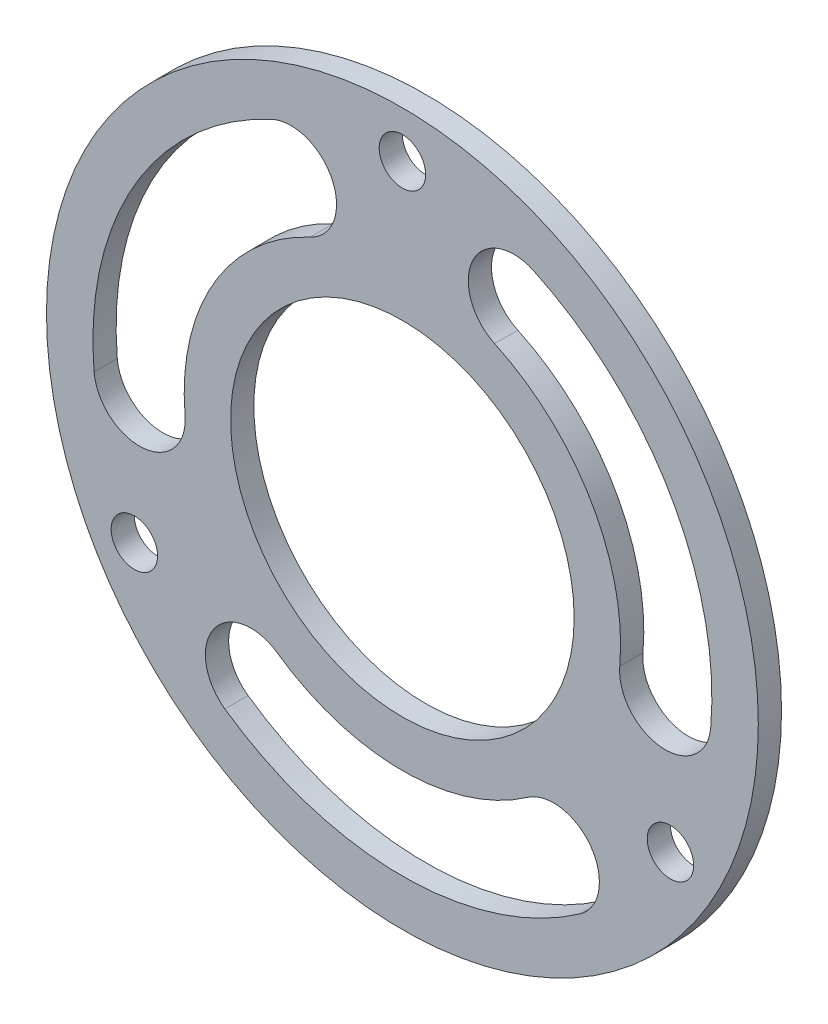
SolidWorks part; units mm, degrees
material "Thornel Mat VMA"
ref_plane "前视基准面" through (0, 0, 0) normal (0, 0, 1) x (1, 0, 0)
ref_plane "上视基准面" through (0, 0, 0) normal (0, 1, 0) x (1, 0, 0)
ref_plane "右视基准面" through (0, 0, 0) normal (1, 0, 0) x (0, 0, -1)
sketch "草图1" plane through (0, 0, 0) normal (0, 0, 1) x (1, 0, 0)
  line L3 (0, 20) -> (0, 0) construction
  circle A0 centre (0, 0) radius 23
  circle A2 centre (0, 20) radius 1.5
  circle A5 centre (0, 0) radius 11.1
  circle A8 centre (0, 0) radius 20 construction
  circle A16 centre (17.3205, -10) radius 1.5
  circle A17 centre (-17.3205, -10) radius 1.5
  dimension "D1" = 46
  dimension "D4" = 3
  dimension "D7" = 3
  dimension "D6" = 22.2
  dimension "D5" = 40
extrude "凸台-拉伸1" add sketch "草图1" along normal blind 1.5
sketch "草图2" plane through (0, 0, 1.5) normal (0, 0, 1) x (1, 0, 0)
  line L0 (0, 0) -> (-16.9851, -1.486) construction
  line L1 (-7.2056, 15.4525) -> (0, 0) construction
  line L2 (-17.3205, -10) -> (0, 0) construction
  line L3 (0, 0) -> (0, 20) construction
  arc A0 (-7.2056, 15.4525) -> (-16.9851, -1.486) centre (0, 0) ccw construction
  arc A1 (-8.4524, 18.1262) -> (-19.9239, -1.7431) centre (0, 0) ccw
  arc A2 (-5.9589, 12.7789) -> (-14.0463, -1.2289) centre (0, 0) ccw
  arc A3 (-5.9589, 12.7789) -> (-8.4524, 18.1262) centre (-7.2056, 15.4525) ccw
  arc A4 (-19.9239, -1.7431) -> (-14.0463, -1.2289) centre (-16.9851, -1.486) ccw
  circle A5 centre (0, 0) radius 11.1 construction
  circle A6 centre (0, 0) radius 23 construction
  arc A7 (16.9851, -1.486) -> (7.2056, 15.4525) centre (0, 0) ccw construction
  arc A20 (19.9239, -1.7431) -> (8.4524, 18.1262) centre (0, 0) ccw
  arc A21 (14.0463, -1.2289) -> (5.9589, 12.7789) centre (0, 0) ccw
  arc A22 (14.0463, -1.2289) -> (19.9239, -1.7431) centre (16.9851, -1.486) ccw
  arc A23 (8.4524, 18.1262) -> (5.9589, 12.7789) centre (7.2056, 15.4525) ccw
  arc A24 (-9.7795, -13.9665) -> (9.7795, -13.9665) centre (0, 0) ccw construction
  arc A25 (-11.4715, -16.383) -> (11.4715, -16.383) centre (0, 0) ccw
  arc A26 (-8.0874, -11.55) -> (8.0874, -11.55) centre (0, 0) ccw
  arc A27 (-8.0874, -11.55) -> (-11.4715, -16.383) centre (-9.7795, -13.9665) ccw
  arc A28 (11.4715, -16.383) -> (8.0874, -11.55) centre (9.7795, -13.9665) ccw
  point P4 (-14.7657, 8.525)
  point P24 (14.7657, 8.525)
  point P32 (0, -17.05)
  dimension "D1" = 3
  dimension "D2" = 3
  dimension "D5" = 3
  dimension "D3" = 25
  dimension "D4" = 25
extrude "切除-拉伸1" cut sketch "草图2" against normal through all
